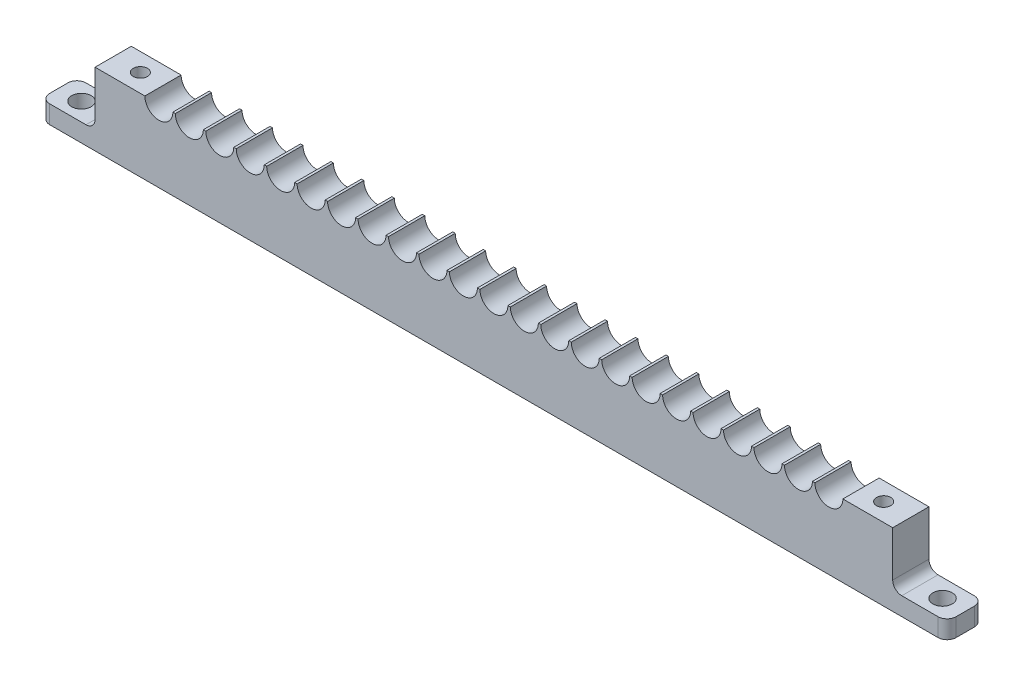
SolidWorks part; units mm, degrees
ref_plane "Front Plane" through (0, 0, 0) normal (0, 0, 1) x (1, 0, 0)
ref_plane "Top Plane" through (0, 0, 0) normal (0, 1, 0) x (1, 0, 0)
ref_plane "Right Plane" through (0, 0, 0) normal (1, 0, 0) x (0, 0, -1)
sketch "Sketch1" plane through (0, 0, 0) normal (0, 0, 1) x (1, 0, 0)
  line L1 (69.85, -6.35) -> (-69.85, -6.35)
  line L2 (69.85, -6.35) -> (69.85, 6.35)
  line L3 (69.85, 6.35) -> (-69.85, 6.35)
  line L4 (-69.85, -6.35) -> (-69.85, 6.35)
  line L5 (69.85, -6.35) -> (-69.85, 6.35) construction
  line L6 (69.85, 6.35) -> (-69.85, -6.35) construction
  point P0 (0, 0)
  dimension "D1" = 139.7
  dimension "D2" = 12.7
extrude "Boss-Extrude1" add sketch "Sketch1" along normal blind 6.35
sketch "Sketch2" plane through (0, 0, 6.35) normal (0, 0, 1) x (1, 0, 0)
  line L0 (-69.85, 6.35) -> (69.85, 6.35) construction
  line L1 (-69.85, 6.35) -> (-69.85, -6.35) construction
  line L2 (69.85, -6.35) -> (69.85, 6.35) construction
  line L3 (0, 6.35) -> (0, -6.35) construction
  line L4 (69.85, 6.35) -> (-69.85, 6.35) construction
  line L5 (-69.85, -6.35) -> (69.85, -6.35) construction
  circle A0 centre (0, 6.35) radius 2.4511
  circle A1 centre (5.334, 6.35) radius 2.4511
  circle A2 centre (10.668, 6.35) radius 2.4511
  circle A3 centre (16.002, 6.35) radius 2.4511
  circle A4 centre (21.336, 6.35) radius 2.4511
  circle A5 centre (26.67, 6.35) radius 2.4511
  circle A6 centre (32.004, 6.35) radius 2.4511
  circle A7 centre (37.338, 6.35) radius 2.4511
  circle A8 centre (42.672, 6.35) radius 2.4511
  circle A9 centre (48.006, 6.35) radius 2.4511
  circle A10 centre (53.34, 6.35) radius 2.4511
  circle A11 centre (58.674, 6.35) radius 2.4511
  circle A13 centre (0, 6.35) radius 2.4511
  circle A14 centre (5.334, 6.35) radius 2.4511
  circle A15 centre (10.668, 6.35) radius 2.4511
  circle A16 centre (16.002, 6.35) radius 2.4511
  circle A17 centre (21.336, 6.35) radius 2.4511
  circle A18 centre (26.67, 6.35) radius 2.4511
  circle A19 centre (32.004, 6.35) radius 2.4511
  circle A20 centre (37.338, 6.35) radius 2.4511
  circle A21 centre (42.672, 6.35) radius 2.4511
  circle A22 centre (48.006, 6.35) radius 2.4511
  circle A23 centre (53.34, 6.35) radius 2.4511
  circle A25 centre (-5.334, 6.35) radius 2.4511
  circle A26 centre (0, 6.35) radius 2.4511
  circle A27 centre (5.334, 6.35) radius 2.4511
  circle A28 centre (10.668, 6.35) radius 2.4511
  circle A29 centre (16.002, 6.35) radius 2.4511
  circle A30 centre (21.336, 6.35) radius 2.4511
  circle A31 centre (26.67, 6.35) radius 2.4511
  circle A32 centre (32.004, 6.35) radius 2.4511
  circle A33 centre (37.338, 6.35) radius 2.4511
  circle A34 centre (42.672, 6.35) radius 2.4511
  circle A35 centre (48.006, 6.35) radius 2.4511
  circle A37 centre (-10.668, 6.35) radius 2.4511
  circle A38 centre (-5.334, 6.35) radius 2.4511
  circle A39 centre (0, 6.35) radius 2.4511
  circle A40 centre (5.334, 6.35) radius 2.4511
  circle A41 centre (10.668, 6.35) radius 2.4511
  circle A42 centre (16.002, 6.35) radius 2.4511
  circle A43 centre (21.336, 6.35) radius 2.4511
  circle A44 centre (26.67, 6.35) radius 2.4511
  circle A45 centre (32.004, 6.35) radius 2.4511
  circle A46 centre (37.338, 6.35) radius 2.4511
  circle A47 centre (42.672, 6.35) radius 2.4511
  circle A49 centre (-16.002, 6.35) radius 2.4511
  circle A50 centre (-10.668, 6.35) radius 2.4511
  circle A51 centre (-5.334, 6.35) radius 2.4511
  circle A52 centre (0, 6.35) radius 2.4511
  circle A53 centre (5.334, 6.35) radius 2.4511
  circle A54 centre (10.668, 6.35) radius 2.4511
  circle A55 centre (16.002, 6.35) radius 2.4511
  circle A56 centre (21.336, 6.35) radius 2.4511
  circle A57 centre (26.67, 6.35) radius 2.4511
  circle A58 centre (32.004, 6.35) radius 2.4511
  circle A59 centre (37.338, 6.35) radius 2.4511
  circle A61 centre (-21.336, 6.35) radius 2.4511
  circle A62 centre (-16.002, 6.35) radius 2.4511
  circle A63 centre (-10.668, 6.35) radius 2.4511
  circle A64 centre (-5.334, 6.35) radius 2.4511
  circle A65 centre (0, 6.35) radius 2.4511
  circle A66 centre (5.334, 6.35) radius 2.4511
  circle A67 centre (10.668, 6.35) radius 2.4511
  circle A68 centre (16.002, 6.35) radius 2.4511
  circle A69 centre (21.336, 6.35) radius 2.4511
  circle A70 centre (26.67, 6.35) radius 2.4511
  circle A71 centre (32.004, 6.35) radius 2.4511
  circle A73 centre (-26.67, 6.35) radius 2.4511
  circle A74 centre (-21.336, 6.35) radius 2.4511
  circle A75 centre (-16.002, 6.35) radius 2.4511
  circle A76 centre (-10.668, 6.35) radius 2.4511
  circle A77 centre (-5.334, 6.35) radius 2.4511
  circle A78 centre (0, 6.35) radius 2.4511
  circle A79 centre (5.334, 6.35) radius 2.4511
  circle A80 centre (10.668, 6.35) radius 2.4511
  circle A81 centre (16.002, 6.35) radius 2.4511
  circle A82 centre (21.336, 6.35) radius 2.4511
  circle A83 centre (26.67, 6.35) radius 2.4511
  circle A85 centre (-32.004, 6.35) radius 2.4511
  circle A86 centre (-26.67, 6.35) radius 2.4511
  circle A87 centre (-21.336, 6.35) radius 2.4511
  circle A88 centre (-16.002, 6.35) radius 2.4511
  circle A89 centre (-10.668, 6.35) radius 2.4511
  circle A90 centre (-5.334, 6.35) radius 2.4511
  circle A91 centre (0, 6.35) radius 2.4511
  circle A92 centre (5.334, 6.35) radius 2.4511
  circle A93 centre (10.668, 6.35) radius 2.4511
  circle A94 centre (16.002, 6.35) radius 2.4511
  circle A95 centre (21.336, 6.35) radius 2.4511
  circle A97 centre (-37.338, 6.35) radius 2.4511
  circle A98 centre (-32.004, 6.35) radius 2.4511
  circle A99 centre (-26.67, 6.35) radius 2.4511
  circle A100 centre (-21.336, 6.35) radius 2.4511
  circle A101 centre (-16.002, 6.35) radius 2.4511
  circle A102 centre (-10.668, 6.35) radius 2.4511
  circle A103 centre (-5.334, 6.35) radius 2.4511
  circle A104 centre (0, 6.35) radius 2.4511
  circle A105 centre (5.334, 6.35) radius 2.4511
  circle A106 centre (10.668, 6.35) radius 2.4511
  circle A107 centre (16.002, 6.35) radius 2.4511
  circle A109 centre (-42.672, 6.35) radius 2.4511
  circle A110 centre (-37.338, 6.35) radius 2.4511
  circle A111 centre (-32.004, 6.35) radius 2.4511
  circle A112 centre (-26.67, 6.35) radius 2.4511
  circle A113 centre (-21.336, 6.35) radius 2.4511
  circle A114 centre (-16.002, 6.35) radius 2.4511
  circle A115 centre (-10.668, 6.35) radius 2.4511
  circle A116 centre (-5.334, 6.35) radius 2.4511
  circle A117 centre (0, 6.35) radius 2.4511
  circle A118 centre (5.334, 6.35) radius 2.4511
  circle A119 centre (10.668, 6.35) radius 2.4511
  circle A121 centre (-48.006, 6.35) radius 2.4511
  circle A122 centre (-42.672, 6.35) radius 2.4511
  circle A123 centre (-37.338, 6.35) radius 2.4511
  circle A124 centre (-32.004, 6.35) radius 2.4511
  circle A125 centre (-26.67, 6.35) radius 2.4511
  circle A126 centre (-21.336, 6.35) radius 2.4511
  circle A127 centre (-16.002, 6.35) radius 2.4511
  circle A128 centre (-10.668, 6.35) radius 2.4511
  circle A129 centre (-5.334, 6.35) radius 2.4511
  circle A130 centre (0, 6.35) radius 2.4511
  circle A131 centre (5.334, 6.35) radius 2.4511
  circle A133 centre (-53.34, 6.35) radius 2.4511
  circle A134 centre (-48.006, 6.35) radius 2.4511
  circle A135 centre (-42.672, 6.35) radius 2.4511
  circle A136 centre (-37.338, 6.35) radius 2.4511
  circle A137 centre (-32.004, 6.35) radius 2.4511
  circle A138 centre (-26.67, 6.35) radius 2.4511
  circle A139 centre (-21.336, 6.35) radius 2.4511
  circle A140 centre (-16.002, 6.35) radius 2.4511
  circle A141 centre (-10.668, 6.35) radius 2.4511
  circle A142 centre (-5.334, 6.35) radius 2.4511
  circle A143 centre (0, 6.35) radius 2.4511
  circle A157 centre (-5.334, 6.35) radius 2.4511
  circle A158 centre (-10.668, 6.35) radius 2.4511
  circle A159 centre (-16.002, 6.35) radius 2.4511
  circle A160 centre (-21.336, 6.35) radius 2.4511
  circle A161 centre (-26.67, 6.35) radius 2.4511
  circle A162 centre (-32.004, 6.35) radius 2.4511
  circle A163 centre (-37.338, 6.35) radius 2.4511
  circle A164 centre (-42.672, 6.35) radius 2.4511
  circle A165 centre (-48.006, 6.35) radius 2.4511
  circle A166 centre (-53.34, 6.35) radius 2.4511
  circle A167 centre (-58.674, 6.35) radius 2.4511
  dimension "D1" = 4.9022
  dimension "D2" = 12
  dimension "D3" = 12
extrude "Cut-Extrude1" cut sketch "Sketch2" against normal through all
hole_wizard "Tap Drill for M3x0.5 Tap1" positions "Sketch3" profile "Sketch4" hole size "M3x0.5" standard "ANSI Metric" end condition through all
sketch "Sketch3" plane through (0, 6.35, 0) normal (0, 1, 0) x (1, 0, 0)
  point P0 (-65.0875, -3.175)
  point P3 (65.0875, -3.175)
sketch "Sketch4" plane through (-65.0875, 6.35, 3.175) normal (1, 0, 0) x (0, 0, 1)
  line L0 (0, 0) -> (0, 12.7)
  line L1 (0, 12.7) -> (1.25, 12.7)
  line L2 (1.25, 12.7) -> (1.25, 0)
  line L5 (1.25, 0) -> (0, 0)
  line L11 (0, -6.35) -> (0, 107.95) construction
  dimension "Thru Hole Dia." = 2.5
  dimension "Thru Hole Depth" = 12.7
sketch "Sketch5" plane through (0, -6.35, 0) normal (0, -1, 0) x (1, 0, 0)
  line L0 (-69.85, 0) -> (69.85, 0) construction
  line L1 (-69.85, 6.35) -> (-79.375, 6.35)
  line L2 (-69.85, 6.35) -> (-69.85, 0)
  line L3 (-69.85, 0) -> (-79.375, 0)
  line L4 (-79.375, 6.35) -> (-79.375, 0)
  dimension "D1" = 9.525
extrude "Boss-Extrude2" add sketch "Sketch5" against normal blind 3.175
fillet "Fillet1" radius 1.5875 1 edges at (-69.85, -3.175, 3.175)
hole_wizard "M3 Clearance Hole1" positions "Sketch6" profile "Sketch7" hole size "M3" standard "ANSI Metric" end condition through all
sketch "Sketch6" plane through (0, -3.175, 0) normal (0, 1, 0) x (1, 0, 0)
  line L0 (-75.4062, 0) -> (-75.4062, -6.35) construction
  line L1 (-79.375, 0) -> (-71.4375, 0) construction
  line L2 (-71.4375, -6.35) -> (-79.375, -6.35) construction
  point P9 (-75.4062, -3.175)
sketch "Sketch7" plane through (-75.4062, -3.175, 3.175) normal (1, 0, 0) x (0, 0, 1)
  line L0 (0, 0) -> (0, 3.175)
  line L1 (0, 3.175) -> (1.7, 3.175)
  line L2 (1.7, 3.175) -> (1.7, 0)
  line L5 (1.7, 0) -> (0, 0)
  line L11 (0, -6.35) -> (0, 107.95) construction
  dimension "Thru Hole Dia." = 3.4
  dimension "Thru Hole Depth" = 3.175
fillet "Fillet2" radius 1.5875 2 edges at (-79.375, -4.7625, 0) (-79.375, -4.7625, 6.35)
mirror "Mirror5" about plane through (0, 0, 0) normal (1, 0, 0) of "Fillet2", "M3 Clearance Hole1", "Boss-Extrude2"
fillet "Fillet3" radius 1.5875 1 edges at (69.85, -3.175, 3.175)
